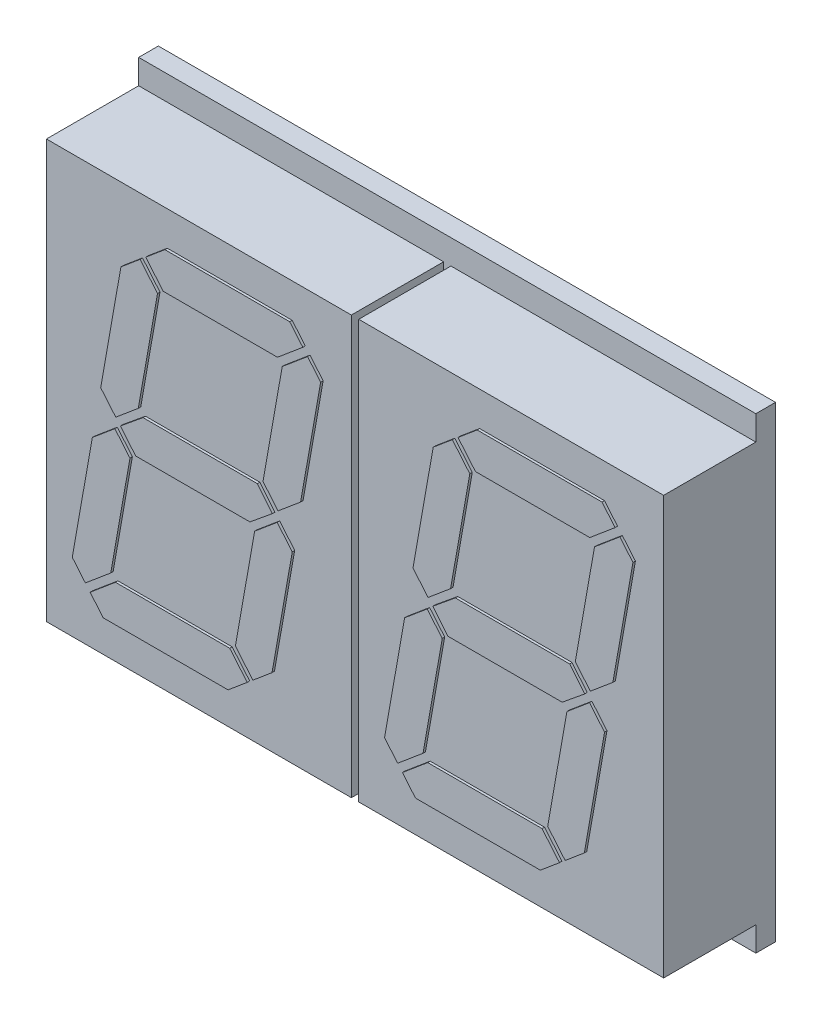
SolidWorks part; units mm, degrees
ref_plane "Спереди" through (0, 0, 0) normal (0, 0, 1) x (1, 0, 0)
ref_plane "Сверху" through (0, 0, 0) normal (0, 1, 0) x (1, 0, 0)
ref_plane "Справа" through (0, 0, 0) normal (1, 0, 0) x (0, 0, -1)
sketch "Эскиз1" plane through (0, 0, 0) normal (0, 0, 1) x (1, 0, 0)
  line L1 (-12.55, -9.5) -> (12.55, -9.5)
  line L2 (-12.55, -9.5) -> (-12.55, 9.5)
  line L3 (-12.55, 9.5) -> (12.55, 9.5)
  line L4 (12.55, -9.5) -> (12.55, 9.5)
  line L5 (-12.55, -9.5) -> (12.55, 9.5) construction
  line L6 (-12.55, 9.5) -> (12.55, -9.5) construction
  point P0 (0, 0)
  dimension "D1" = 25.1
  dimension "D2" = 19
extrude "Бобышка-Вытянуть1" add sketch "Эскиз1" along normal blind 0.8
sketch "Эскиз2" plane through (0, 0, 0.8) normal (0, 0, 1) x (1, 0, 0)
  line L1 (-12.55, 8.5) -> (-0.15, 8.5)
  line L2 (-12.55, 8.5) -> (-12.55, -8.5)
  line L3 (-12.55, -8.5) -> (-0.15, -8.5)
  line L4 (-0.15, 8.5) -> (-0.15, -8.5)
  line L5 (-12.55, 9.5) -> (-12.55, -9.5) construction
  line L6 (0, 9.5) -> (0, -9.5) construction
  line L7 (12.55, 9.5) -> (-12.55, 9.5) construction
  line L8 (-12.55, -9.5) -> (12.55, -9.5) construction
  line L9 (12.55, -8.5) -> (0.15, -8.5)
  line L10 (0.15, 8.5) -> (0.15, -8.5)
  line L11 (12.55, 8.5) -> (0.15, 8.5)
  line L12 (12.55, 8.5) -> (12.55, -8.5)
  point P7 (-12.55, 0)
  dimension "D1" = 0.3
  dimension "D2" = 17
extrude "Бобышка-Вытянуть2" add sketch "Эскиз2" along normal blind 3.75
sketch "Эскиз3" plane through (0, 0, 4.55) normal (0, 0, 1) x (1, 0, 0)
  line L0 (-2.0247, 6.4752) -> (-2.5574, 7.1101)
  line L1 (-8.4136, 6.4565) -> (-7.6347, 7.1101)
  line L2 (-2.5574, 7.1101) -> (-7.6347, 7.1101)
  line L3 (-1.2988, 5.6103) -> (-2.1154, 0.9797)
  line L4 (-2.8623, 5.3804) -> (-3.6449, 0.9427)
  line L5 (-7.9333, 5.4174) -> (-8.7158, 0.9797)
  line L6 (-3.0552, 5.6103) -> (-7.7035, 5.6103)
  line L7 (-8.5231, 0.75) -> (-3.8748, 0.75)
  line L8 (-7.9333, 5.4174) -> (-8.6437, 6.2638)
  line L9 (-9.4224, 5.6103) -> (-8.6437, 6.2638)
  line L10 (-7.7035, 5.6103) -> (-8.4136, 6.4565)
  line L11 (-1.2988, 5.6103) -> (-1.8318, 6.2456)
  line L12 (-2.8623, 5.3804) -> (-1.8318, 6.2456)
  line L13 (-3.0552, 5.6103) -> (-2.0247, 6.4752)
  line L14 (-9.4224, 5.6103) -> (-10.2451, 0.9429)
  line L15 (-4.1764, -0.7498) -> (-3.2605, 0)
  line L16 (-3.9841, -0.98) -> (-3.0678, -0.2114)
  line L17 (-2.4544, -0.9426) -> (-3.0678, -0.2114)
  line L18 (-8.8248, -0.7498) -> (-9.4389, 0)
  line L19 (-9.0546, -0.9427) -> (-9.6683, -0.2112)
  line L20 (-8.8248, -0.7498) -> (-4.1764, -0.7498)
  line L21 (-4.0561, -6.2634) -> (-3.2775, -5.6098)
  line L22 (-4.9965, -5.6099) -> (-9.6444, -5.6099)
  line L23 (-4.7666, -5.4168) -> (-4.0561, -6.2634)
  line L24 (-5.0649, -7.1101) -> (-4.2862, -6.4563)
  line L25 (-4.9965, -5.6099) -> (-4.2862, -6.4563)
  line L26 (-3.9841, -0.98) -> (-4.7666, -5.4168)
  line L27 (-2.4544, -0.9426) -> (-3.2775, -5.6098)
  line L28 (-9.8372, -5.3796) -> (-10.8682, -6.2448)
  line L29 (-10.8682, -6.2448) -> (-11.401, -5.6099)
  line L30 (-10.1422, -7.1101) -> (-10.675, -6.4751)
  line L31 (-10.5844, -0.9795) -> (-11.401, -5.6099)
  line L32 (-9.0546, -0.9427) -> (-9.8372, -5.3796)
  line L33 (-9.6444, -5.6099) -> (-10.675, -6.4751)
  line L34 (-5.0649, -7.1101) -> (-10.1422, -7.1101)
  line L35 (-10.5844, -0.9795) -> (-9.6683, -0.2112)
  line L36 (-3.2605, 0) -> (-3.8748, 0.75)
  line L37 (-3.0315, 0.2114) -> (-3.6449, 0.9427)
  line L38 (-3.0315, 0.2114) -> (-2.1154, 0.9797)
  line L39 (-9.4389, 0) -> (-8.5231, 0.75)
  line L40 (-9.6318, 0.2114) -> (-10.2451, 0.9429)
  line L41 (-9.6318, 0.2114) -> (-8.7158, 0.9797)
  line L42 (-9.4389, 0) -> (-3.2605, 0) construction
  line L43 (-12.55, 0) -> (12.55, 0) construction
  line L44 (-12.55, 8.5) -> (-12.55, -8.5) construction
  line L47 (10.6756, 6.4752) -> (10.1428, 7.1101)
  line L48 (4.2866, 6.4565) -> (5.0655, 7.1101)
  line L49 (10.1428, 7.1101) -> (5.0655, 7.1101)
  line L50 (11.4015, 5.6103) -> (10.5848, 0.9797)
  line L51 (9.838, 5.3804) -> (9.0554, 0.9427)
  line L52 (4.7669, 5.4174) -> (3.9845, 0.9797)
  line L53 (9.6451, 5.6103) -> (4.9968, 5.6103)
  line L54 (4.1772, 0.75) -> (8.8255, 0.75)
  line L55 (4.7669, 5.4174) -> (4.0566, 6.2638)
  line L56 (3.2779, 5.6103) -> (4.0566, 6.2638)
  line L57 (4.9968, 5.6103) -> (4.2866, 6.4565)
  line L58 (11.4015, 5.6103) -> (10.8685, 6.2456)
  line L59 (9.838, 5.3804) -> (10.8685, 6.2456)
  line L60 (9.6451, 5.6103) -> (10.6756, 6.4752)
  line L61 (3.2779, 5.6103) -> (2.4552, 0.9429)
  line L62 (8.5239, -0.7498) -> (9.4398, 0)
  line L63 (8.7162, -0.98) -> (9.6325, -0.2114)
  line L64 (10.2459, -0.9426) -> (9.6325, -0.2114)
  line L65 (3.8755, -0.7498) -> (3.2614, 0)
  line L66 (3.6456, -0.9427) -> (3.0319, -0.2112)
  line L67 (3.8755, -0.7498) -> (8.5239, -0.7498)
  line L68 (8.6442, -6.2634) -> (9.4228, -5.6098)
  line L69 (7.7038, -5.6099) -> (3.0559, -5.6099)
  line L70 (7.9337, -5.4168) -> (8.6442, -6.2634)
  line L71 (7.6354, -7.1101) -> (8.4141, -6.4563)
  line L72 (7.7038, -5.6099) -> (8.4141, -6.4563)
  line L73 (8.7162, -0.98) -> (7.9337, -5.4168)
  line L74 (10.2459, -0.9426) -> (9.4228, -5.6098)
  line L75 (2.8631, -5.3796) -> (1.8321, -6.2448)
  line L76 (1.8321, -6.2448) -> (1.2993, -5.6099)
  line L77 (2.5581, -7.1101) -> (2.0253, -6.4751)
  line L78 (2.1159, -0.9795) -> (1.2993, -5.6099)
  line L79 (3.6456, -0.9427) -> (2.8631, -5.3796)
  line L80 (3.0559, -5.6099) -> (2.0253, -6.4751)
  line L81 (7.6354, -7.1101) -> (2.5581, -7.1101)
  line L82 (2.1159, -0.9795) -> (3.0319, -0.2112)
  line L83 (9.4398, 0) -> (8.8255, 0.75)
  line L84 (9.6688, 0.2114) -> (9.0554, 0.9427)
  line L85 (9.6688, 0.2114) -> (10.5848, 0.9797)
  line L86 (3.2614, 0) -> (4.1772, 0.75)
  line L87 (3.0685, 0.2114) -> (2.4552, 0.9429)
  line L88 (3.0685, 0.2114) -> (3.9845, 0.9797)
  line L89 (3.2614, 0) -> (9.4398, 0) construction
  point P1 (6.3503, 0)
  point P68 (-6.3497, 0)
  point P75 (-6.35, 0)
  point P93 (6.3506, 0)
  point P94 (6.3503, 0)
extrude "Бобышка-Вытянуть3" add sketch "Эскиз3" along normal blind 0.1
